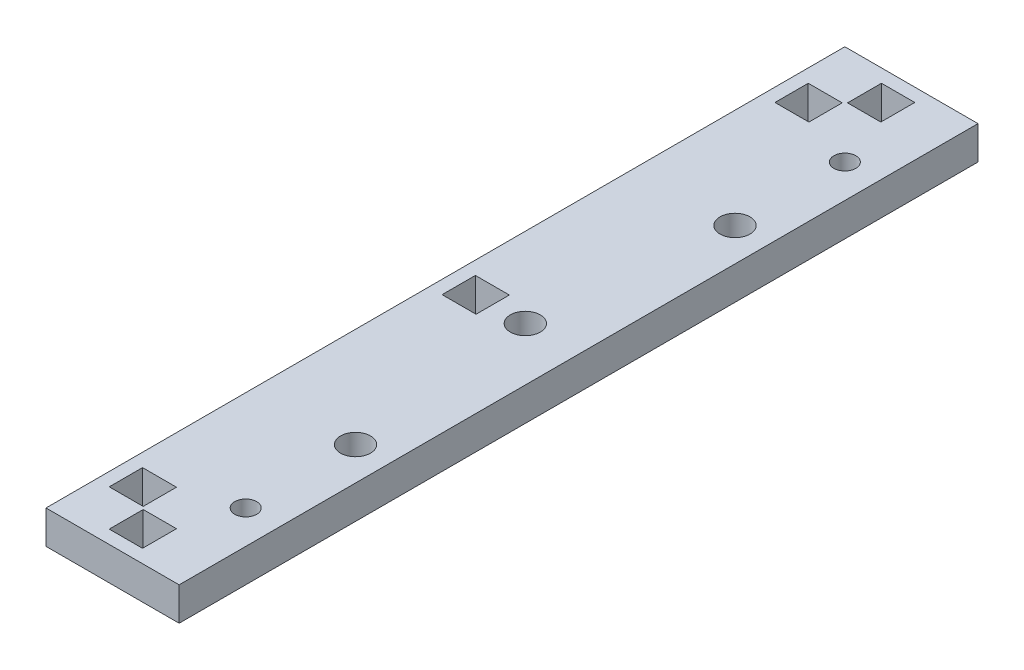
SolidWorks part; units mm, degrees
ref_plane "Front" through (0, 0, 0) normal (0, 0, 1) x (1, 0, 0)
ref_plane "Top" through (0, 0, 0) normal (0, 1, 0) x (1, 0, 0)
ref_plane "Right" through (0, 0, 0) normal (1, 0, 0) x (0, 0, -1)
sketch "Sketch1" plane through (0, 0, 0) normal (0, 1, 0) x (1, 0, 0)
  line L1 (-10, -60) -> (10, -60)
  line L2 (-10, -60) -> (-10, 60)
  line L3 (-10, 60) -> (10, 60)
  line L4 (10, -60) -> (10, 60)
  line L5 (-10, -60) -> (10, 60) construction
  line L6 (-10, 60) -> (10, -60) construction
  point P0 (0, 0)
  dimension "D1" = 20
  dimension "D2" = 120
extrude "Boss-Extrude1" add sketch "Sketch1" along normal blind 5
hole_wizard "Ø3.3 (3.3) Diameter Hole1" positions "Sketch3" profile "Sketch2" hole size "Ø3.3" standard "ANSI Metric" end condition through all
sketch "Sketch3" plane through (0, 5, 0) normal (0, 1, 0) x (1, 0, 0)
  line L2 (5, -45) -> (5, 45)
  line L7 (-10, 60) -> (-10, -60) construction
  line L9 (10, 60) -> (-10, 60) construction
  point P0 (5, 45)
  point P6 (5, -45)
  dimension "D1" = 90
  dimension "D2" = 15
  dimension "D3" = 15
sketch "Sketch2" plane through (5, 5, -45) normal (1, 0, 0) x (0, 0, 1)
  line L0 (0, 0) -> (0, 5)
  line L1 (0, 5) -> (1.65, 5)
  line L2 (1.65, 5) -> (1.65, 0)
  line L5 (1.65, 0) -> (0, 0)
  line L11 (0, -6.35) -> (0, 107.95) construction
  dimension "Thru Hole Dia." = 3.3
  dimension "Thru Hole Depth" = 5
sketch "Sketch5" plane through (0, 5, 0) normal (0, 1, 0) x (1, 0, 0)
  line L0 (-10, 60) -> (-10, -60) construction
  line L1 (-8, 52.5) -> (-2.9, 52.5)
  line L2 (-8, 52.5) -> (-8, 47.5)
  line L3 (-8, 47.5) -> (-2.9, 47.5)
  line L4 (-2.9, 52.5) -> (-2.9, 47.5)
  line L5 (-8, -47.5) -> (-2.9, -47.5)
  line L6 (-8, -47.5) -> (-8, -52.5)
  line L7 (-8, -52.5) -> (-2.9, -52.5)
  line L8 (-2.9, -47.5) -> (-2.9, -52.5)
  line L9 (-2.5, -52.9) -> (2.5, -52.9)
  line L10 (-2.5, -52.9) -> (-2.5, -58)
  line L11 (-2.5, -58) -> (2.5, -58)
  line L12 (2.5, -52.9) -> (2.5, -58)
  line L17 (-2.5, 58) -> (2.5, 58)
  line L18 (-2.5, 58) -> (-2.5, 52.9)
  line L19 (-2.5, 52.9) -> (2.5, 52.9)
  line L20 (2.5, 58) -> (2.5, 52.9)
  line L33 (10, 60) -> (-10, 60) construction
  line L35 (-10, -60) -> (10, -60) construction
  line L37 (-8, 2.5) -> (-2.9, 2.5)
  line L38 (-8, 2.5) -> (-8, -2.5)
  line L39 (-8, -2.5) -> (-2.9, -2.5)
  line L40 (-2.9, 2.5) -> (-2.9, -2.5)
  dimension "D1" = 2
  dimension "D2" = 95
  dimension "D3" = 105
  dimension "D4" = 7.5
  dimension "D5" = 5.1
  dimension "D6" = 5
  dimension "D8" = 2
  dimension "D9" = 5.1
  dimension "D10" = 2
  dimension "D11" = 5.1
  dimension "D14" = 7.5
  dimension "D15" = 5
  dimension "D16" = 45
extrude "Cut-Extrude1" cut sketch "Sketch5" against normal through all
hole_wizard "Ø4.5 (4.5) Diameter Hole2" positions "Sketch9" profile "Sketch8" hole size "Ø4.5" standard "ANSI Metric" end condition through all
sketch "Sketch9" plane through (0, 5, 0) normal (0, 1, 0) x (1, 0, 0)
  line L0 (-4.6341, 0) -> (35.4105, 0) construction
  line L2 (2, -6.8848) -> (2, 49993.1152) construction
  line L3 (10, -60) -> (10, 60) construction
  point P0 (5, 28.5)
  point P2 (2, 0)
  point P4 (5, -28.5)
  dimension "D1" = 57
  dimension "D2" = 28.5
  dimension "D3" = 3
  dimension "D4" = 8
sketch "Sketch8" plane through (5, 5, -28.5) normal (1, 0, 0) x (0, 0, 1)
  line L0 (0, 0) -> (0, 5)
  line L1 (0, 5) -> (2.25, 5)
  line L2 (2.25, 5) -> (2.25, 0)
  line L5 (2.25, 0) -> (0, 0)
  line L11 (0, -6.35) -> (0, 107.95) construction
  dimension "Thru Hole Dia." = 4.5
  dimension "Thru Hole Depth" = 5
